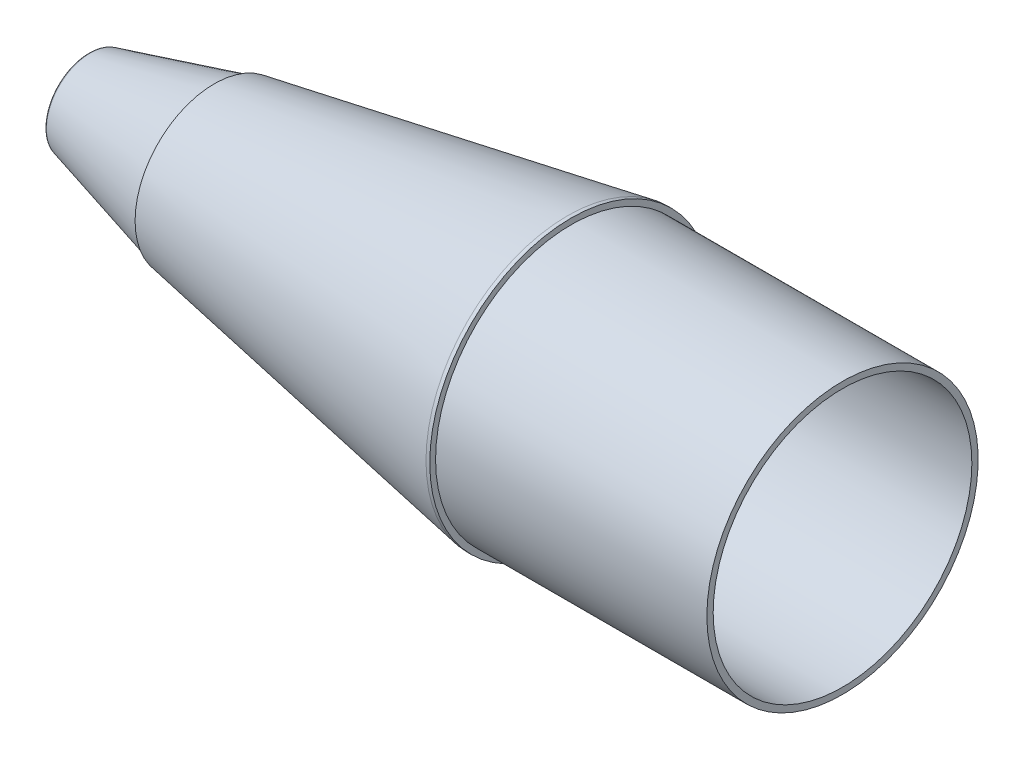
SolidWorks part; units mm, degrees
material "6061-T6 (SS)"
ref_plane "Front Plane" through (0, 0, 0) normal (0, 0, 1) x (1, 0, 0)
ref_plane "Top Plane" through (0, 0, 0) normal (0, 1, 0) x (1, 0, 0)
ref_plane "Right Plane" through (0, 0, 0) normal (1, 0, 0) x (0, 0, -1)
sketch "Sketch1" plane through (0, 0, 0) normal (0, 0, 1) x (1, 0, 0)
  line L1 (25.31, 15.9385) -> (96.399, 28.4734)
  line L2 (96.399, 28.4734) -> (97.161, 28.4734)
  line L3 (97.161, 28.4734) -> (97.161, 27.305)
  line L4 (97.161, 27.305) -> (151.771, 27.305)
  line L5 (151.771, 27.305) -> (151.771, 26.035)
  line L6 (151.771, 26.035) -> (91.3465, 26.035)
  line L9 (0, 0) -> (0, 8.7376)
  line L13 (27.94, 0) -> (0, 0)
  line L15 (0, 0) -> (151.771, 0) construction
  line L16 (25.31, 15.9385) -> (25.31, 15.5194)
  line L17 (25.31, 15.5194) -> (0, 8.7376)
  line L18 (91.3465, 26.035) -> (27.94, 14.8547)
  line L19 (27.94, 14.8547) -> (27.94, 0)
  dimension "D2" = 27.94
  dimension "D3" = 1.27
  dimension "D4" = 28.4734
  dimension "D5" = 15.9385
  dimension "D6" = 15
  dimension "D7" = 27.305
  dimension "D8" = 15.5194
  dimension "D9" = 0.762
  dimension "D10" = 54.61
  dimension "D11" = 8.7376
  dimension "D12" = 10
  dimension "D13" = 1.524
revolve "Revolve1" add sketch "Sketch1" angle 360 about L15
fillet "Fillet1" radius 1.5494 1 edges at (27.94, 0, 14.8547)
hole_wizard "F (0.257) Diameter Hole1" positions "Sketch2" profile "Sketch3" hole size "F" standard "ANSI Inch"
sketch "Sketch2" plane through (27.94, 0, 0) normal (1, 0, 0) x (0, 0, -1)
  point P0 (0, 0)
sketch "Sketch3" plane through (27.94, 0, 0) normal (0, 1, 0) x (0, 0, -1)
  line L0 (0, 0) -> (0, 15.875)
  line L1 (0, 15.875) -> (3.2639, 13.9139)
  line L2 (3.2639, 13.9139) -> (3.2639, 0)
  line L5 (3.2639, 0) -> (0, 0)
  line L10 (0, 15.875) -> (-3.2639, 13.9139) construction
  line L11 (0, -6.35) -> (0, 107.95) construction
  dimension "Hole Dia." = 6.5278
  dimension "Hole Depth" = 15.875
  dimension "Drill Angle" = 118
fillet "Fillet2" radius 0.508 1 edges at (0, 0, 8.7376)
sketch "Sketch4" plane through (0, 0, 0) normal (-1, 0, 0) x (0, 0, 1)
  circle A0 centre (0, 0) radius 7.366
  dimension "D1" = 14.732
extrude "Cut-Extrude1" cut sketch "Sketch4" against normal blind 24.13 draft 15 draft outward yes
fillet "Fillet3" radius 0.254 1 edges at (24.13, 0, 13.8316)
sketch "Sketch5" plane through (0, 0, 0) normal (1, 0, 0) x (0, 0, -1)
  circle A0 centre (0, 0) radius 8.0264
  dimension "D1" = 16.0528
extrude "Cut-Extrude2" cut sketch "Sketch5" along normal up to next
